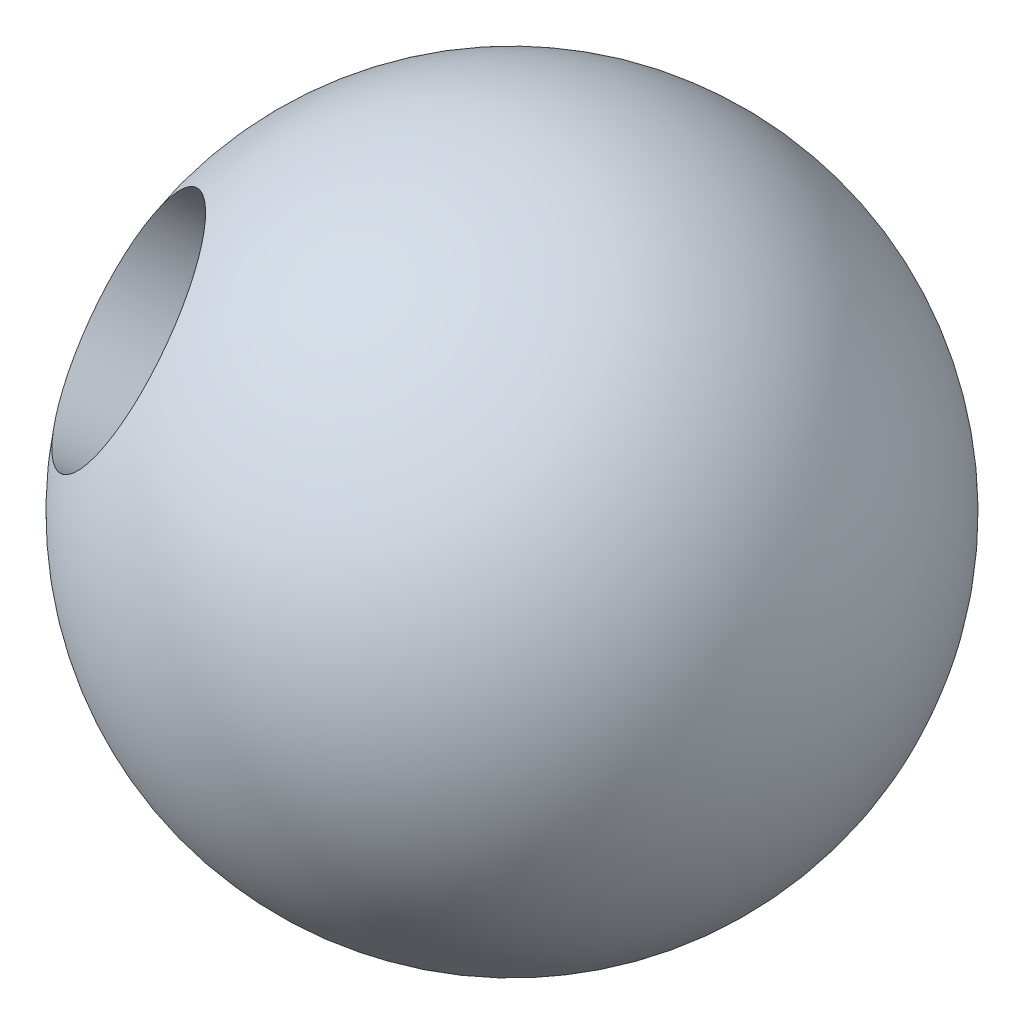
SolidWorks part; units mm, degrees
ref_plane "Front Plane" through (0, 0, 0) normal (0, 0, 1) x (1, 0, 0)
ref_plane "Top Plane" through (0, 0, 0) normal (0, 1, 0) x (1, 0, 0)
ref_plane "Right Plane" through (0, 0, 0) normal (1, 0, 0) x (0, 0, -1)
sketch "Sketch1" plane through (0, 0, 0) normal (0, 0, 1) x (1, 0, 0)
  line L0 (0, 15) -> (0, -15)
  arc A0 (0, -15) -> (0, 15) centre (0, 0) ccw
  dimension "D1" = 15
revolve "Revolve1" add sketch "Sketch1" angle 360 about L0
hole_wizard "M12x1.75 Tapped Hole1" positions "3DSketch1" profile "Sketch2" tap size "M12x1.75" standard "ANSI Metric"
sketch3d "3DSketch1"
  point P0 (0, 0, 0)
  point P3 (-9.617, 7.2622, 8.9316)
sketch "Sketch2" plane through (-9.617, 7.2622, 8.9316) normal (0.7658, 0.4548, 0.4548) x (0.0506, -0.7475, 0.6623)
  line L0 (0, 0) -> (0, 16.5644)
  line L1 (0, 16.5644) -> (5.1, 13.5)
  line L2 (5.1, 13.5) -> (5.1, 0)
  line L5 (5.1, 0) -> (0, 0)
  line L10 (0, 16.5644) -> (-5.1, 13.5) construction
  line L11 (0, -6.35) -> (0, 107.95) construction
  dimension "Tap Drill Dia." = 10.2
  dimension "Tap Drill Depth" = 13.5
  dimension "Drill Angle" = 118
cosmetic thread "Hole Thread1" parameters "D1"=6, "D2"=12
cosmetic thread "Hole Thread2" parameters "D1"=6, "D2"=12
